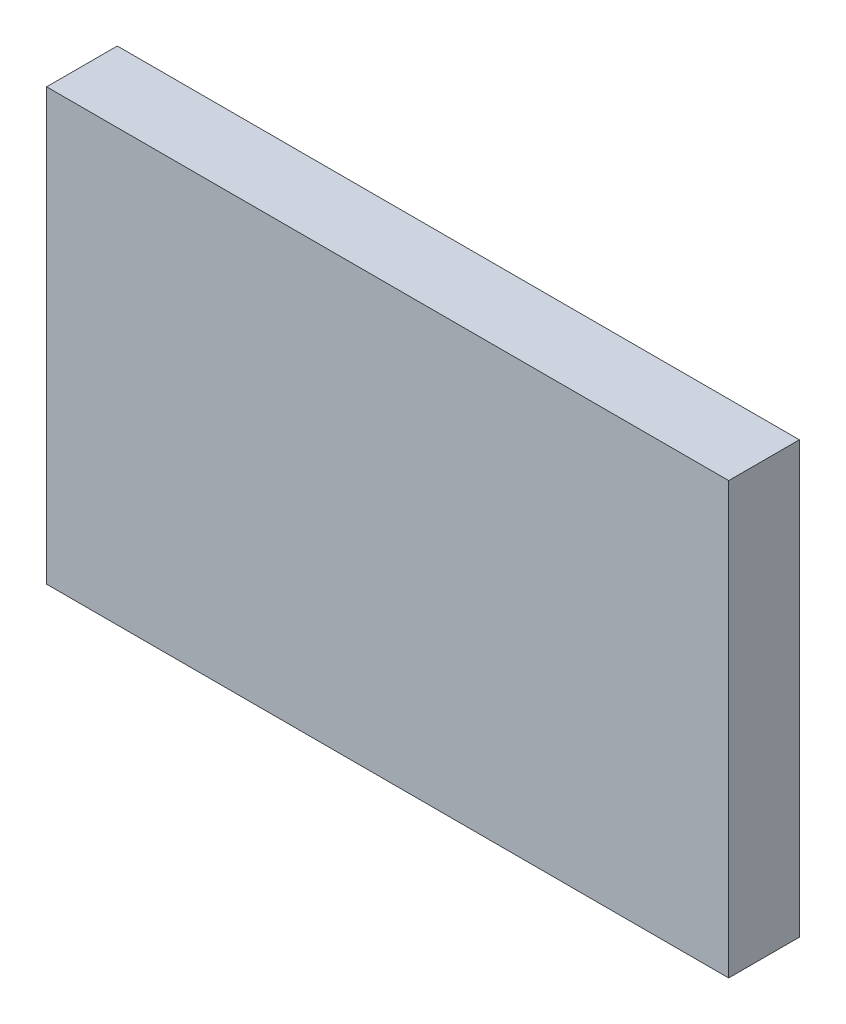
SolidWorks part; units mm, degrees
ref_plane "Front Plane" through (0, 0, 0) normal (0, 0, 1) x (1, 0, 0)
ref_plane "Top Plane" through (0, 0, 0) normal (0, 1, 0) x (1, 0, 0)
ref_plane "Right Plane" through (0, 0, 0) normal (1, 0, 0) x (0, 0, -1)
sketch "Sketch1" plane through (0, 0, 0) normal (0, 0, 1) x (1, 0, 0)
  line L0 (-4.826, 3.048) -> (4.826, 3.048)
  line L1 (4.826, 3.048) -> (4.826, -3.048)
  line L2 (4.826, -3.048) -> (-4.826, -3.048)
  line L3 (-4.826, -3.048) -> (-4.826, 3.048)
extrude "Component_Outline" add sketch "Sketch1" along normal blind 1 separate body
sketch3d "3DSketch1"
  line L0 (0, 0, 0) -> (1, 0, 0)
  line L1 (0, 0, 0) -> (0, 1, 0)
  line L2 (0, 0, 0) -> (0, 0, 1)
  point P0 (0, 0, 0)
